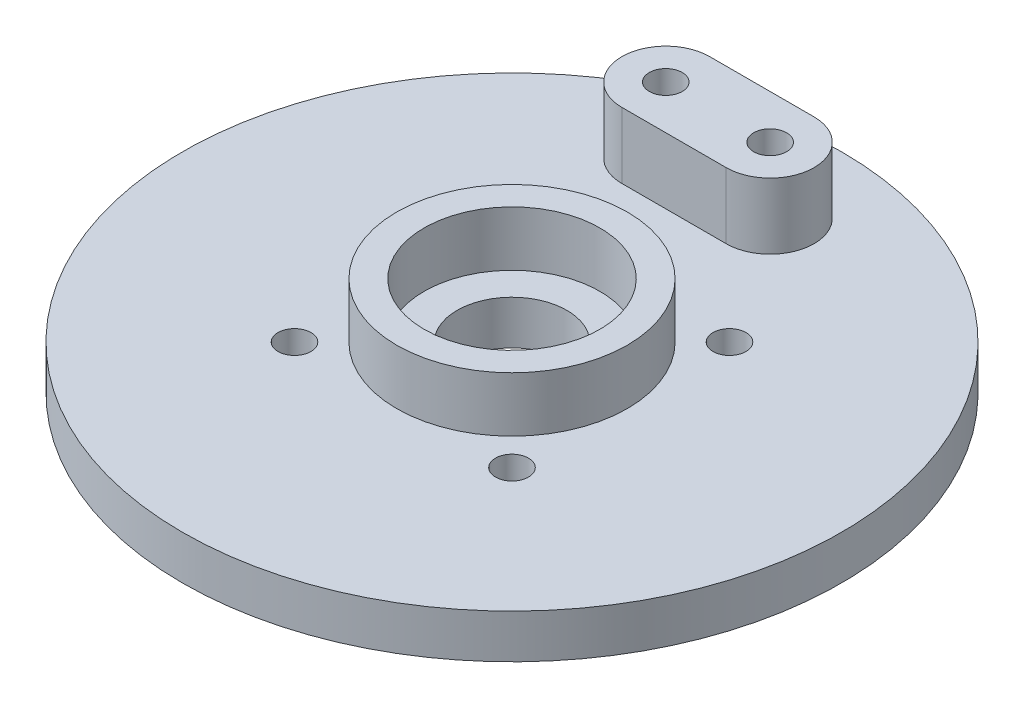
SolidWorks part; units mm, degrees
ref_plane "Front" through (0, 0, 0) normal (0, 0, 1) x (1, 0, 0)
ref_plane "Top" through (0, 0, 0) normal (0, 1, 0) x (1, 0, 0)
ref_plane "Right" through (0, 0, 0) normal (1, 0, 0) x (0, 0, -1)
sketch "Sketch1" plane through (0, 0, 0) normal (0, 1, 0) x (1, 0, 0)
  circle A0 centre (0, 0) radius 30
  circle A1 centre (0, 0) radius 5
  dimension "D1" = 60
  dimension "D2" = 10
extrude "Boss-Extrude1" add sketch "Sketch1" along normal blind 4
sketch "Sketch4" plane through (0, 4, 0) normal (0, 1, 0) x (1, 0, 0)
  circle A0 centre (0, 0) radius 8
  circle A1 centre (0, 0) radius 10.5
  dimension "D1" = 16
  dimension "D2" = 2.5
extrude "Boss-Extrude2" add sketch "Sketch4" along normal blind 5
sketch "Sketch5" plane through (0, 4, 0) normal (0, 1, 0) x (1, 0, 0)
  line L7 (14.5977, 15.4464) -> (14.5977, 4.9464)
  line L8 (-5.4023, 25.4464) -> (14.5977, 25.4464)
  line L9 (-5.4023, 25.4464) -> (-5.4023, 15.4464)
  line L10 (-5.4023, 15.4464) -> (14.5977, 15.4464)
  line L11 (14.5977, 25.4464) -> (14.5977, 15.4464)
  line L12 (-5.4023, 25.4464) -> (14.5977, 15.4464) construction
  line L13 (-5.4023, 15.4464) -> (14.5977, 25.4464) construction
  line L14 (14.09, 7.0565) -> (-3.9023, 15.4464)
  circle A1 centre (14.09, 7.0565) radius 2.1703
  point P16 (4.5977, 20.4464)
  dimension "D7" = 1.5
  dimension "D4" = 10
  dimension "D5" = 20
  dimension "D6" = 10.5
  dimension "D8" = 25
sketch "Sketch6" plane through (0, 4, 0) normal (0, 1, 0) x (1, 0, 0)
  line L0 (0, 0) -> (0, 30) construction
  line L1 (0, 0) -> (-30, 0) construction
  circle A0 centre (-7.5, 21.5) radius 1.5
  circle A1 centre (2, 21.5) radius 1.5
  circle A2 centre (0, 0) radius 30 construction
  dimension "D1" = 3
  dimension "D2" = 3
  dimension "D3" = 9.5
  dimension "D4" = 7.5
  dimension "D5" = 21.5
extrude "Cut-Extrude3" cut sketch "Sketch6" against normal through all
sketch "Sketch7" plane through (0, 4, 0) normal (0, 1, 0) x (1, 0, 0)
  line L0 (2, 25.5) -> (-7.5, 25.5)
  line L1 (-7.5, 17.5) -> (2, 17.5)
  circle A0 centre (-7.5, 21.5) radius 1.5 construction
  circle A2 centre (-7.5, 21.5) radius 1.5
  circle A3 centre (2, 21.5) radius 1.5
  arc A4 (2, 17.5) -> (2, 25.5) centre (2, 21.5) ccw
  arc A5 (-7.5, 25.5) -> (-7.5, 17.5) centre (-7.5, 21.5) ccw
  circle A6 centre (2, 21.5) radius 4 construction
  circle A7 centre (-7.5, 21.5) radius 4 construction
  dimension "D2" = 4
  dimension "D1" = 9.5
extrude "Boss-Extrude3" add sketch "Sketch7" along normal blind 6
sketch "Sketch8" plane through (0, 4, 0) normal (0, 1, 0) x (1, 0, 0)
  line L0 (0, 0) -> (-9.8995, 9.8995) construction
  line L1 (0, 0) -> (-10.5, 0) construction
  circle A0 centre (-9.8995, 9.8995) radius 1.5
  circle A1 centre (0, 0) radius 10.5 construction
  circle A2 centre (0, 0) radius 10.5 construction
  circle A3 centre (9.8995, 9.8995) radius 1.5
  circle A4 centre (9.8995, -9.8995) radius 1.5
  circle A5 centre (-9.8995, -9.8995) radius 1.5
  point P18 (0, 0)
  dimension "D2" = 3
  dimension "D1" = 14
  dimension "D3" = 45
  dimension "D4" = 4
extrude "Cut-Extrude4" cut sketch "Sketch8" against normal through all
